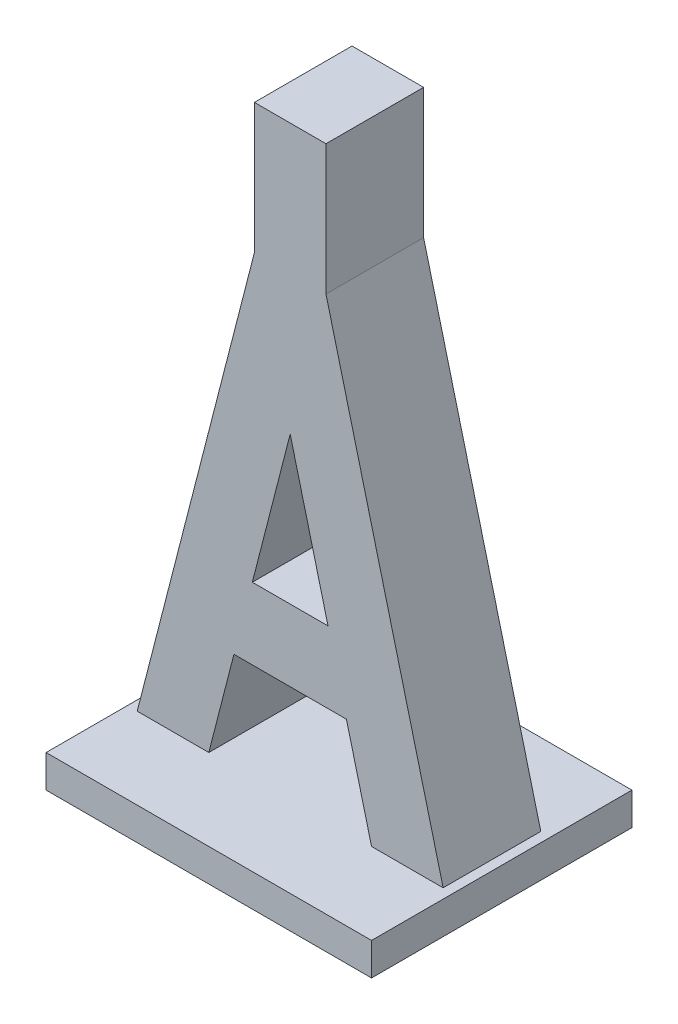
SolidWorks part; units mm, degrees
ref_plane "Vorne" through (0, 0, 0) normal (0, 0, 1) x (1, 0, 0)
ref_plane "Oben" through (0, 0, 0) normal (0, 1, 0) x (1, 0, 0)
ref_plane "Rechts" through (0, 0, 0) normal (1, 0, 0) x (0, 0, -1)
sketch "Skizze1" plane through (0, 0, 0) normal (0, 0, 1) x (1, 0, 0)
  line L0 (0, 72.7011) -> (0, -93.9396) construction
  line L1 (8.6429, 0) -> (-8.6429, 0)
  line L2 (-8.6429, 0) -> (-12.5, -15)
  line L3 (-12.5, -15) -> (-23.5, -15)
  line L4 (-23.5, -15) -> (-5.5, 55)
  line L5 (-5.5, 55) -> (5.5, 55)
  line L7 (0, 33.6111) -> (-5.8143, 11)
  line L8 (-5.8143, 11) -> (5.8143, 11)
  line L9 (0, 33.6111) -> (5.8143, 11)
  line L10 (23.5, -15) -> (5.5, 55)
  line L11 (12.5, -15) -> (23.5, -15)
  line L12 (8.6429, 0) -> (12.5, -15)
  point P13 (0, 11)
  point P17 (0, 0)
  dimension "D1" = 47
  dimension "D2" = 70
  dimension "D3" = 11
  dimension "D4" = 11
  dimension "D5" = 11
  dimension "D6" = 15
extrude "Aufsatz-Linear austragen1" add sketch "Skizze1" along normal blind 15
sketch "Skizze2" plane through (0, -15, 0) normal (0, -1, 0) x (1, 0, 0)
  line L0 (-33.8133, 7.5) -> (34.2436, 7.5) construction
  line L1 (0, 21.6468) -> (0, -6.2201) construction
  line L2 (-23.5, 0) -> (-12.5, 0) construction
  line L3 (-23.5, 15) -> (-12.5, 15) construction
  line L5 (-25, 27.5) -> (25, 27.5)
  line L6 (-25, 27.5) -> (-25, -12.5)
  line L7 (-25, -12.5) -> (25, -12.5)
  line L8 (25, 27.5) -> (25, -12.5)
  dimension "D1" = 50
  dimension "D2" = 40
extrude "Aufsatz-Linear austragen2" add sketch "Skizze2" along normal blind 5
sketch "Skizze3" plane through (0, 0, 15) normal (0, 0, 1) x (1, 0, 0)
  line L0 (0, 78.2186) -> (0, -10.8501) construction
  line L1 (5.5, 55) -> (-5.5, 55)
  line L2 (5.5, 55) -> (-5.5, 55) construction
  line L3 (-5.5, 55) -> (-5.5, 75)
  line L4 (-5.5, 75) -> (5.5, 75)
  line L5 (5.5, 55) -> (5.5, 75)
  point P10 (0, 75)
  point P11 (0, 55)
  dimension "D1" = 20
  dimension "D2" = 11
extrude "Aufsatz-Linear austragen3" add sketch "Skizze3" against normal blind 15
